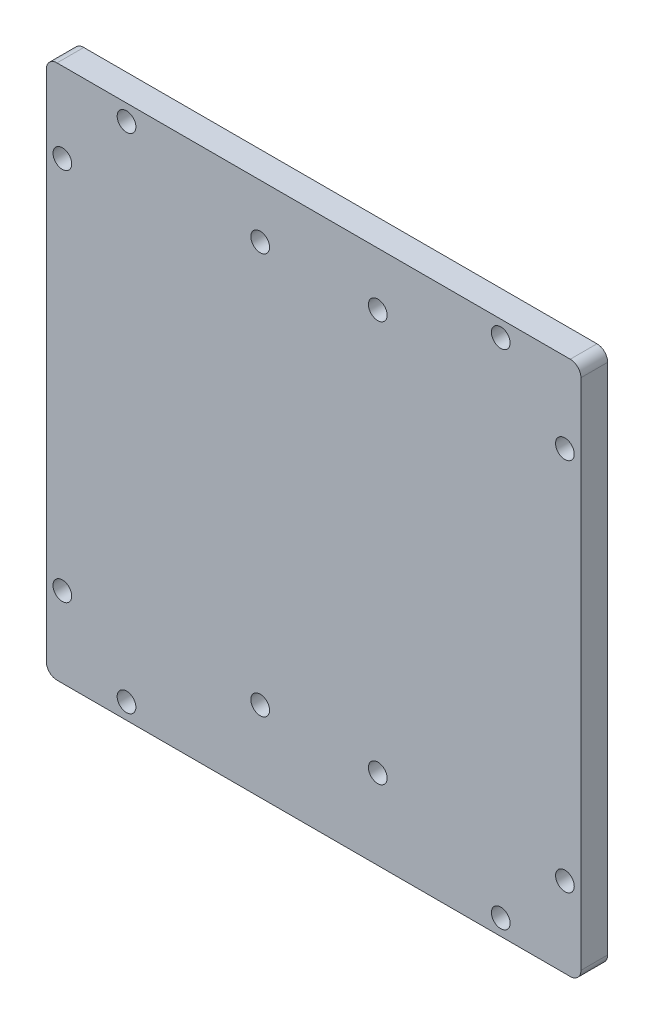
SolidWorks part; units mm, degrees
ref_plane "Спереди" through (0, 0, 0) normal (0, 0, 1) x (1, 0, 0)
ref_plane "Сверху" through (0, 0, 0) normal (0, 1, 0) x (1, 0, 0)
ref_plane "Справа" through (0, 0, 0) normal (1, 0, 0) x (0, 0, -1)
sketch "Эскиз1" plane through (0, 0, 0) normal (0, 0, 1) x (1, 0, 0)
  line L0 (0, 0) -> (27.9829, 0) construction
  line L1 (-48, -50) -> (48, -50)
  line L2 (-50, -48) -> (-50, 48)
  line L3 (-48, 50) -> (48, 50)
  line L4 (50, -48) -> (50, 48)
  line L7 (0, 0) -> (0, -40.6) construction
  circle A0 centre (-47, 35) radius 1.75
  circle A1 centre (47, 35) radius 1.75
  circle A2 centre (47, -35) radius 1.75
  circle A3 centre (-47, -35) radius 1.75
  circle A4 centre (-35, 47) radius 1.75
  circle A5 centre (35, 47) radius 1.75
  circle A6 centre (-35, -47) radius 1.75
  circle A7 centre (35, -47) radius 1.75
  arc A8 (-50, -48) -> (-48, -50) centre (-48, -48) ccw
  arc A9 (48, -50) -> (50, -48) centre (48, -48) ccw
  arc A10 (50, 48) -> (48, 50) centre (48, 48) ccw
  arc A11 (-48, 50) -> (-50, 48) centre (-48, 48) ccw
  circle A12 centre (-10, 40) radius 1.75
  circle A13 centre (12, 40) radius 1.75
  circle A14 centre (-10, -35) radius 1.75
  circle A15 centre (12, -35) radius 1.75
  point P0 (0, 0)
  dimension "D3" = 3.5
  dimension "D6" = 3.5
  dimension "D9" = 2
  dimension "D13" = 22
  dimension "D12" = 40
  dimension "D1" = 3.5
  dimension "D2" = 3.5
  dimension "D4" = 3.5
  dimension "D5" = 3.5
  dimension "D7" = 22
  dimension "D8" = 75
  dimension "D10" = 15
  dimension "D11" = 75
extrude "Бобышка-Вытянуть1" add sketch "Эскиз1" along normal blind 5
